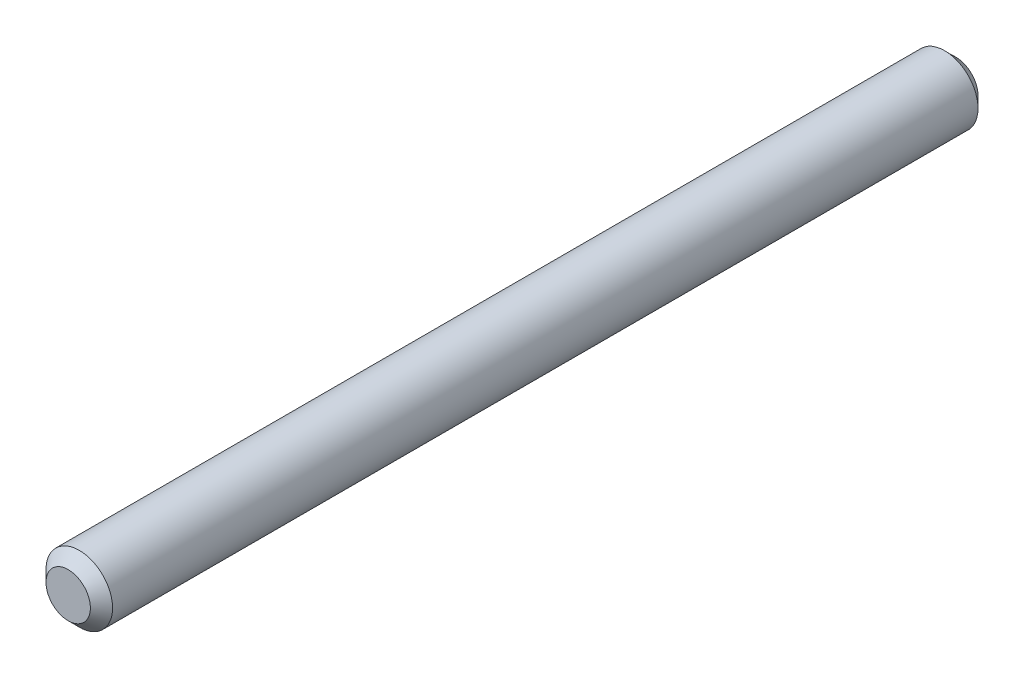
SolidWorks part; units mm, degrees
material "Alloy Steel"
ref_plane "Front Plane" through (0, 0, 0) normal (0, 0, 1) x (1, 0, 0)
ref_plane "Top Plane" through (0, 0, 0) normal (0, 1, 0) x (1, 0, 0)
ref_plane "Right Plane" through (0, 0, 0) normal (1, 0, 0) x (0, 0, -1)
sketch "Sketch1" plane through (0, 0, 0) normal (0, 0, 1) x (1, 0, 0)
  circle A0 centre (0, 0) radius 1.5
  dimension "D1" = 3
extrude "Body" add sketch "Sketch1" along normal mid plane 40
cosmetic thread "Cosmetic Thread1" parameters "D2"=2.439
chamfer "Chamfer1" distance 0.5 angle 45
